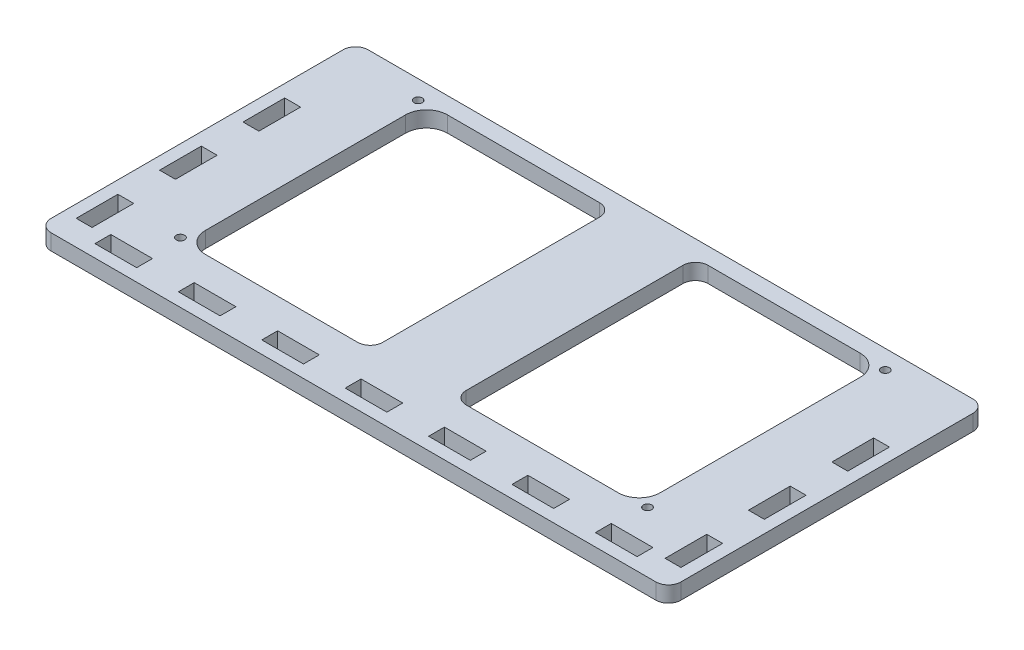
SolidWorks part; units mm, degrees
material "Maple"
ref_plane "Front Plane" through (0, 0, 0) normal (0, 0, 1) x (1, 0, 0)
ref_plane "Top Plane" through (0, 0, 0) normal (0, 1, 0) x (1, 0, 0)
ref_plane "Right Plane" through (0, 0, 0) normal (1, 0, 0) x (0, 0, -1)
sketch "Sketch1" plane through (0, 0, 0) normal (0, 1, 0) x (1, 0, 0)
  line L1 (0, 0) -> (121, 0)
  line L2 (0, 0) -> (0, -66)
  line L3 (0, -66) -> (121, -66)
  line L4 (121, 0) -> (121, -66)
  dimension "D1" = 121
  dimension "D2" = 66
extrude "Boss-Extrude1" add sketch "Sketch1" along normal blind 3.8
sketch "Sketch2" plane through (0, 3.8, 0) normal (0, 1, 0) x (1, 0, 0)
  line L0 (60.5, -66) -> (60.5, 0) construction
  line L2 (6, -4) -> (115, -4)
  line L3 (6, -4) -> (6, -62)
  line L4 (6, -62) -> (115, -62)
  line L5 (115, -4) -> (115, -62)
  line L6 (6, -4) -> (115, -62) construction
  line L7 (6, -62) -> (115, -4) construction
  line L9 (0, -66) -> (121, -66) construction
  line L10 (121, 0) -> (0, 0) construction
  line L11 (0, -33) -> (121, -33) construction
  line L12 (0, 0) -> (0, -66) construction
  line L13 (121, -66) -> (121, 0) construction
  point P4 (60.5, -33)
  dimension "D1" = 29
  dimension "D2" = 54.5
  dimension "D3" = 58
  dimension "D4" = 109
extrude "Cut-Extrude1" cut sketch "Sketch2" against normal through all
fillet "Fillet1" radius 5 4 edges at (6, 1.9, 62) (115, 1.9, 62) (115, 1.9, 4) (6, 1.9, 4)
sketch "Sketch3" plane through (0, 3.8, 0) normal (0, 1, 0) x (1, 0, 0)
  line L0 (60.5, 0) -> (60.5, -66) construction
  line L1 (121, 0) -> (0, 0) construction
  line L2 (0, -66) -> (121, -66) construction
  line L3 (11, -62) -> (110, -62) construction
  line L4 (50.5, -4) -> (70.5, -4)
  line L5 (50.5, -4) -> (50.5, -62)
  line L6 (50.5, -62) -> (70.5, -62)
  line L7 (70.5, -4) -> (70.5, -62)
  line L8 (50.5, -4) -> (70.5, -62) construction
  line L9 (50.5, -62) -> (70.5, -4) construction
  point P6 (60.5, -33)
  dimension "D1" = 20
extrude "Boss-Extrude2" add sketch "Sketch3" against normal through all
fillet "Fillet2" radius 3 4 edges at (70.5, 1.9, 62) (70.5, 1.9, 4) (50.5, 1.9, 62) (50.5, 1.9, 4)
sketch "Sketch4" plane through (0, 3.8, 0) normal (0, 1, 0) x (1, 0, 0)
  line L0 (60.5, -66) -> (60.5, 0) construction
  line L1 (121, -66) -> (121, 0) construction
  line L2 (0, -66) -> (121, -66) construction
  line L3 (121, 0) -> (0, 0) construction
  line L4 (0, 0) -> (0, -66) construction
  line L5 (0, -33) -> (121, -33) construction
  circle A0 centre (116.5, -61.5) radius 1
  circle A1 centre (116.5, -4.5) radius 1
  circle A2 centre (4.5, -4.5) radius 1
  circle A3 centre (4.5, -61.5) radius 1
  dimension "D1" = 2
  dimension "D6" = 2
  dimension "D7" = 2
  dimension "D10" = 2
  dimension "D3" = 28.5
  dimension "D2" = 56
  dimension "D5" = 28.5
  dimension "D4" = 56
  dimension "D11" = 28.5
  dimension "D8" = 28.5
  dimension "D9" = 56
  dimension "D12" = 56
extrude "Cut-Extrude2" cut sketch "Sketch4" against normal through all
sketch "Sketch5" plane through (0, 3.8, 0) normal (0, 1, 0) x (1, 0, 0)
  line L0 (121, 0) -> (0, 0) construction
  line L1 (-15, 0) -> (136, 0)
  line L2 (-15, 0) -> (-15, -76)
  line L3 (-15, -76) -> (136, -76)
  line L4 (136, 0) -> (136, -76)
  line L5 (0, 0) -> (0, -66) construction
  line L6 (121, -66) -> (121, 0) construction
  line L7 (0, -66) -> (121, -66) construction
  line L8 (0, 0) -> (0, -66)
  line L9 (0, -66) -> (121, -66)
  line L10 (121, -66) -> (121, 0)
  line M25 (0, 0) -> (0, -66)
  line M26 (0, -66) -> (121, -66)
  line M27 (121, -66) -> (121, 0)
  dimension "D1" = 15
  dimension "D2" = 15
  dimension "D3" = 10
extrude "Boss-Extrude3" add sketch "Sketch5" against normal through all contours L4 L1 L2 L3 M27 M26 M25
fillet "Fillet3" radius 3 4 edges at (-15, 1.9, 0) (-15, 1.9, 76) (136, 1.9, 76) (136, 1.9, 0)
sketch "Sketch6" plane through (0, 0, 0) normal (0, -1, 0) x (1, 0, 0)
  line L0 (-12, 76) -> (133, 76) construction
  line L1 (133, 20) -> (129.2, 20)
  line L2 (133, 20) -> (133, 30)
  line L3 (133, 30) -> (129.2, 30)
  line L4 (129.2, 20) -> (129.2, 30)
  line L5 (133, 40) -> (129.2, 40)
  line L6 (133, 40) -> (133, 50)
  line L7 (133, 50) -> (129.2, 50)
  line L8 (129.2, 40) -> (129.2, 50)
  line L9 (133, 60) -> (129.2, 60)
  line L10 (133, 60) -> (133, 70)
  line L11 (133, 70) -> (129.2, 70)
  line L12 (129.2, 60) -> (129.2, 70)
  line L13 (125.5, 69.2) -> (115.5, 69.2)
  line L14 (125.5, 69.2) -> (125.5, 73)
  line L15 (125.5, 73) -> (115.5, 73)
  line L16 (115.5, 69.2) -> (115.5, 73)
  line L17 (105.5, 69.2) -> (95.5, 69.2)
  line L18 (105.5, 69.2) -> (105.5, 73)
  line L19 (105.5, 73) -> (95.5, 73)
  line L20 (95.5, 69.2) -> (95.5, 73)
  line L21 (85.5, 69.2) -> (75.5, 69.2)
  line L22 (85.5, 69.2) -> (85.5, 73)
  line L23 (85.5, 73) -> (75.5, 73)
  line L24 (75.5, 69.2) -> (75.5, 73)
  line L25 (65.5, 69.2) -> (55.5, 69.2)
  line L26 (65.5, 69.2) -> (65.5, 73)
  line L27 (65.5, 73) -> (55.5, 73)
  line L28 (55.5, 69.2) -> (55.5, 73)
  line L29 (45.5, 69.2) -> (35.5, 69.2)
  line L30 (45.5, 69.2) -> (45.5, 73)
  line L31 (45.5, 73) -> (35.5, 73)
  line L32 (35.5, 69.2) -> (35.5, 73)
  line L33 (25.5, 69.2) -> (15.5, 69.2)
  line L34 (25.5, 69.2) -> (25.5, 73)
  line L35 (25.5, 73) -> (15.5, 73)
  line L36 (15.5, 69.2) -> (15.5, 73)
  line L37 (5.5, 69.2) -> (-4.5, 69.2)
  line L38 (5.5, 69.2) -> (5.5, 73)
  line L39 (5.5, 73) -> (-4.5, 73)
  line L40 (-4.5, 69.2) -> (-4.5, 73)
  line L41 (-8.2, 60) -> (-12, 60)
  line L42 (-8.2, 60) -> (-8.2, 70)
  line L43 (-8.2, 70) -> (-12, 70)
  line L44 (-12, 60) -> (-12, 70)
  line L45 (-8.2, 40) -> (-12, 40)
  line L46 (-8.2, 40) -> (-8.2, 50)
  line L47 (-8.2, 50) -> (-12, 50)
  line L48 (-12, 40) -> (-12, 50)
  line L49 (-8.2, 20) -> (-12, 20)
  line L50 (-8.2, 20) -> (-8.2, 30)
  line L51 (-8.2, 30) -> (-12, 30)
  line L52 (-12, 20) -> (-12, 30)
  line L53 (60.5, 76) -> (60.5, 0) construction
  line L54 (133, 0) -> (-12, 0) construction
  line L55 (55.5, 71.1) -> (65.5, 71.1) construction
  line L56 (131.1, 70) -> (131.1, 60) construction
  line L58 (131.1, 50) -> (131.1, 40) construction
  line L59 (131.1, 30) -> (131.1, 20) construction
  line L60 (-10.1, 70) -> (-10.1, 60) construction
  line L62 (-10.1, 50) -> (-10.1, 40) construction
  line L63 (-10.1, 30) -> (-10.1, 20) construction
  line L64 (136, 3) -> (136, 73) construction
  line L65 (-15, 3) -> (-15, 73) construction
  dimension "D2" = 3.8
  dimension "D3" = 10
  dimension "D4" = 5
  dimension "D5" = 10
  dimension "D6" = 10
  dimension "D7" = 10
  dimension "D8" = 10
  dimension "D9" = 10
  dimension "D10" = 10
  dimension "D11" = 10
  dimension "D12" = 10
  dimension "D13" = 10
  dimension "D14" = 10
  dimension "D15" = 10
  dimension "D16" = 10
  dimension "D19" = 10
  dimension "D20" = 3.8
  dimension "D21" = 6
  dimension "D22" = 10
  dimension "D23" = 10
  dimension "D24" = 10
  dimension "D25" = 10
  dimension "D18" = 3
  dimension "D26" = 3
  dimension "D17" = 3
extrude "Cut-Extrude3" cut sketch "Sketch6" against normal through all
equation "\"D6@Sketch4\"=\"D1@Sketch4\""
equation "\"D7@Sketch4\"=\"D6@Sketch4\""
equation "\"D10@Sketch4\"=\"D7@Sketch4\""
equation "\"D5@Sketch4\"=\"D3@Sketch4\""
equation "\"D4@Sketch4\"=\"D2@Sketch4\""
equation "\"D11@Sketch4\"=\"D3@Sketch4\""
equation "\"D8@Sketch4\"=\"D11@Sketch4\""
equation "\"D9@Sketch4\"=\"D2@Sketch4\""
equation "\"D12@Sketch4\"=\"D9@Sketch4\""
equation "\"D4@Sketch6\"=\"D3@Sketch6\"/2"
equation "\"D8@Sketch6\"=\"D3@Sketch6\""
equation "\"D9@Sketch6\"=\"D3@Sketch6\""
equation "\"D10@Sketch6\"=\"D5@Sketch6\""
equation "\"D11@Sketch6\"=\"D5@Sketch6\""
equation "\"D12@Sketch6\"=\"D3@Sketch6\""
equation "\"D13@Sketch6\"=\"D3@Sketch6\""
equation "\"D14@Sketch6\"=\"D3@Sketch6\""
equation "\"D15@Sketch6\"=\"D7@Sketch6\""
equation "\"D16@Sketch6\"=\"D3@Sketch6\""
equation "\"D23@Sketch6\"=\"D19@Sketch6\""
equation "\"D24@Sketch6\"=\"D22@Sketch6\""
equation "\"D25@Sketch6\"=\"D19@Sketch6\""
